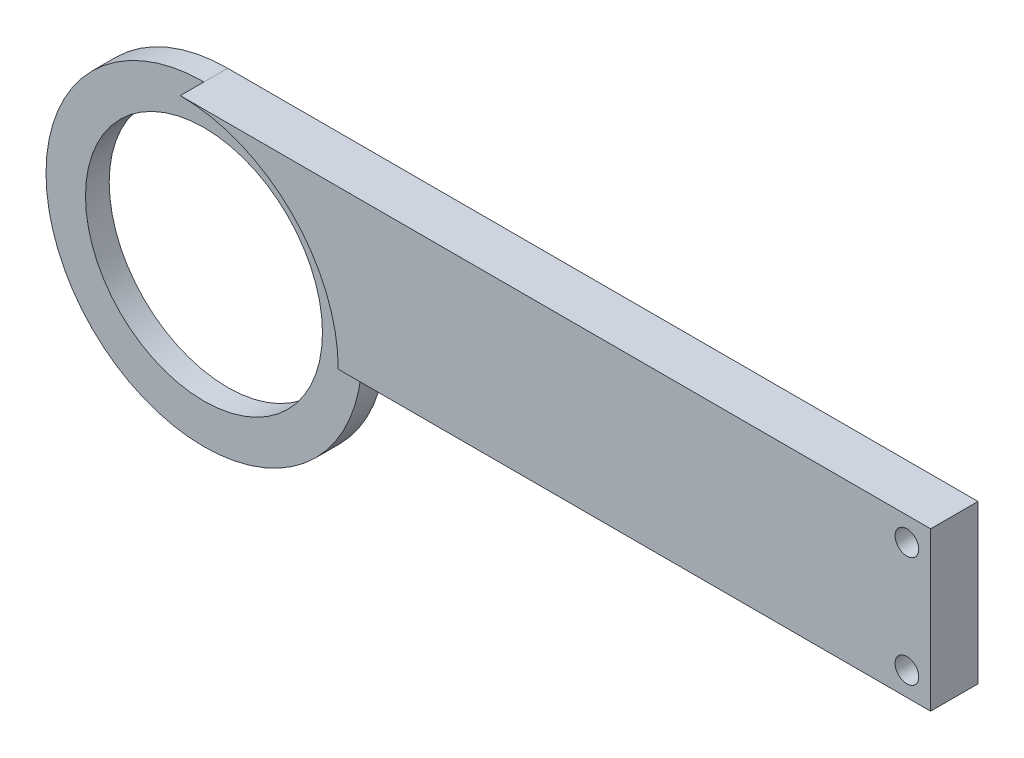
SolidWorks part; units mm, degrees
ref_plane "Plan de face" through (0, 0, 0) normal (0, 0, 1) x (1, 0, 0)
ref_plane "Plan de dessus" through (0, 0, 0) normal (0, 1, 0) x (1, 0, 0)
ref_plane "Plan de droite" through (0, 0, 0) normal (1, 0, 0) x (0, 0, -1)
sketch "Esquisse1" plane through (0, 0, 0) normal (0, 0, 1) x (1, 0, 0)
  line L1 (42.6139, 23.7864) -> (-43.2113, 23.7864)
  line L2 (42.6139, 23.7864) -> (42.6139, 3.7864)
  line L3 (42.6139, 3.7864) -> (-43.2113, 3.7864)
  line L4 (-43.2113, 23.7864) -> (-43.2113, 3.7864)
  circle A0 centre (-43.2113, 3.7864) radius 20
  circle A1 centre (-43.2113, 3.7864) radius 15
  dimension "D2" = 0
  dimension "D3" = 40
  dimension "D1" = 20
extrude "Boss.-Extru.1" add sketch "Esquisse1" along normal blind 6 contours A0 L3 L2 L1 | A1 L4 A0 L3 | A1 L3 A0 L4
sketch "Esquisse2" plane through (0, 0, 6) normal (0, 0, 1) x (1, 0, 0)
  circle A0 centre (-43.2113, 3.7864) radius 15
  circle A1 centre (-43.2113, 3.7864) radius 15 construction
  circle A2 centre (-43.2113, 3.7864) radius 20
  dimension "D1" = 30
  dimension "D2" = 0
extrude "Enlèv. mat.-Extru.1" cut sketch "Esquisse2" against normal blind 3
sketch "Esquisse3" plane through (0, 0, 6) normal (0, 0, 1) x (1, 0, 0)
  line L1 (42.6139, 23.7864) -> (51.7839, 23.7864)
  line L2 (42.6139, 23.7864) -> (42.6139, 3.7864)
  line L3 (42.6139, 3.7864) -> (51.7839, 3.7864)
  line L4 (51.7839, 23.7864) -> (51.7839, 3.7864)
  dimension "D1" = 20
  dimension "D2" = 9.17
extrude "Boss.-Extru.2" add sketch "Esquisse3" against normal blind 6
sketch "Esquisse4" plane through (0, 0, 0) normal (0, 0, -1) x (-1, 0, 0)
  line L0 (-48.7839, 31.2142) -> (-48.7839, -14.3241) construction
  line L1 (-51.7839, 3.7864) -> (-51.7839, 23.7864) construction
  line L2 (-51.7839, 3.7864) -> (23.2113, 3.7864) construction
  line L3 (-51.7839, 23.7864) -> (43.2113, 23.7864) construction
  circle A0 centre (-48.7839, 20.7864) radius 1.5
  circle A1 centre (-48.7839, 6.7864) radius 1.5
  dimension "D1" = 3
  dimension "D2" = 3
  dimension "D4" = 3
  dimension "D5" = 3
  dimension "D3" = 3
extrude "Enlèv. mat.-Extru.2" cut sketch "Esquisse4" against normal blind 10
sketch "Esquisse5" plane through (0, 0, 0) normal (0, 0, -1) x (-1, 0, 0)
  circle A0 centre (43.2113, 3.7864) radius 20
  arc A1 (23.2113, 3.7864) -> (43.2113, 23.7864) centre (43.2113, 3.7864) ccw construction
  dimension "D1" = 0
  dimension "D2" = 40
